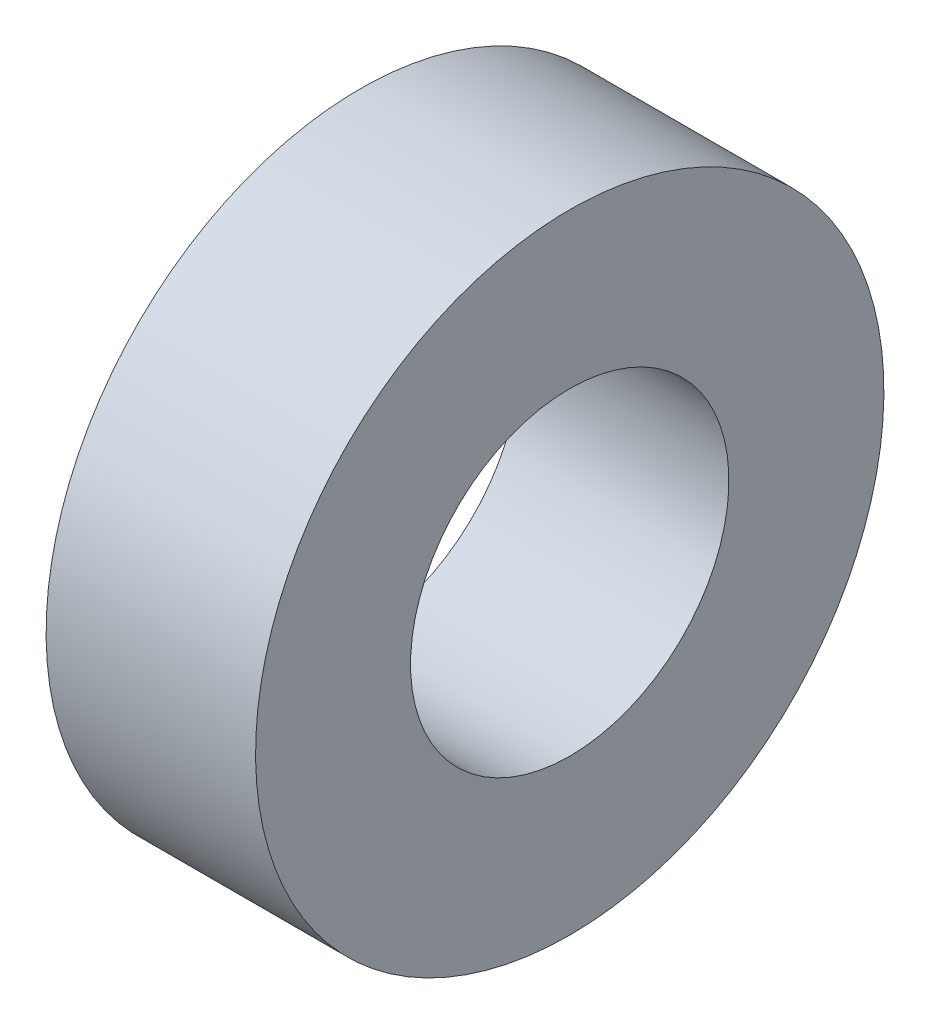
SolidWorks part; units mm, degrees
material "Plain Carbon Steel"
ref_plane "Front Plane" through (0, 0, 0) normal (0, 0, 1) x (1, 0, 0)
ref_plane "Top Plane" through (0, 0, 0) normal (0, 1, 0) x (1, 0, 0)
ref_plane "Right Plane" through (0, 0, 0) normal (1, 0, 0) x (0, 0, -1)
sketch "Sketch1" plane through (0, 0, 0) normal (0, 0, 1) x (1, 0, 0)
  line L0 (0, 0) -> (3.175, 0) construction
  line L1 (0, 4.7625) -> (3.175, 4.7625)
  line L2 (0, 4.7625) -> (0, 2.413)
  line L3 (0, 2.413) -> (3.175, 2.413)
  line L4 (3.175, 4.7625) -> (3.175, 2.413)
  dimension "D1" = 4.826
  dimension "D2" = 3.175
  dimension "D3" = 9.525
revolve "Revolve1" add sketch "Sketch1" angle 360 about L0
